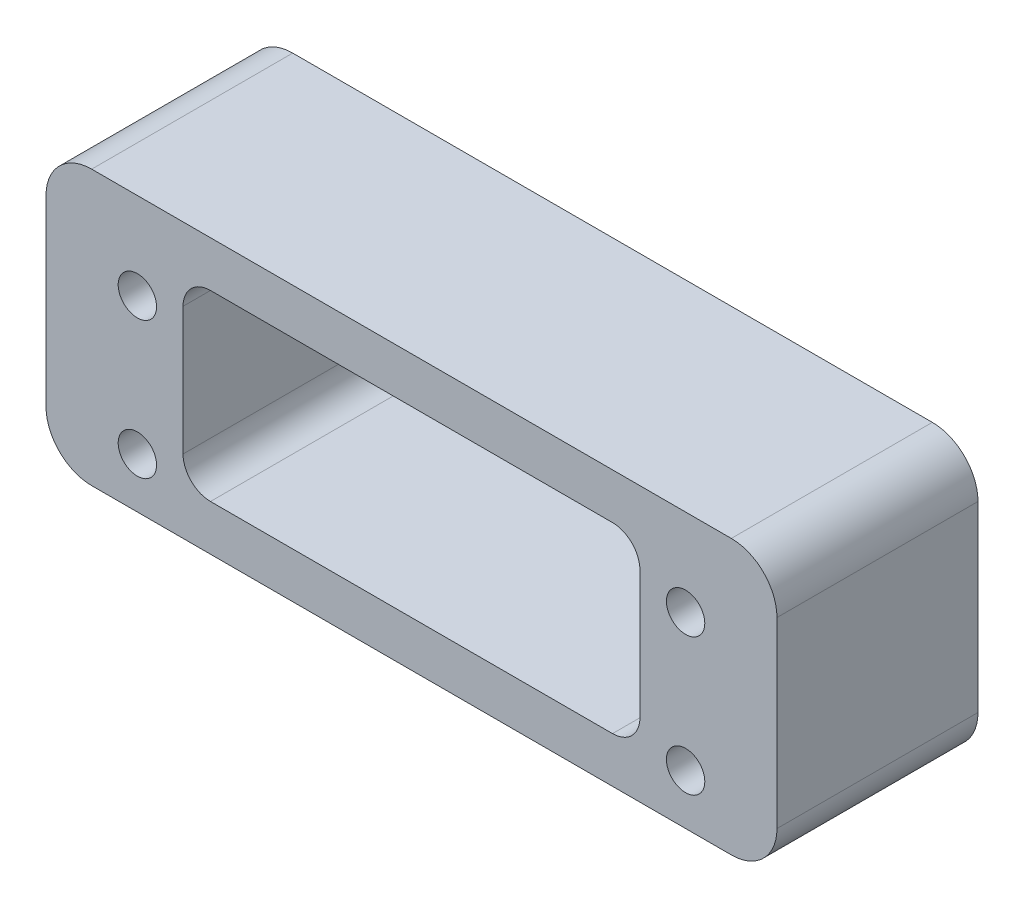
SolidWorks part; units mm, degrees
material "ABS"
ref_plane "前视基准面" through (0, 0, 0) normal (0, 0, 1) x (1, 0, 0)
ref_plane "上视基准面" through (0, 0, 0) normal (0, 1, 0) x (1, 0, 0)
ref_plane "右视基准面" through (0, 0, 0) normal (1, 0, 0) x (0, 0, -1)
sketch "草图1" plane through (0, 0, 0) normal (0, 0, 1) x (1, 0, 0)
  line L1 (-40, 15) -> (40, 15)
  line L2 (-40, 15) -> (-40, -15)
  line L3 (-40, -15) -> (40, -15)
  line L4 (40, 15) -> (40, -15)
  line L5 (-40, 15) -> (40, -15) construction
  line L6 (-40, -15) -> (40, 15) construction
  point P0 (0, 0)
  dimension "D1" = 80
  dimension "D2" = 30
extrude "凸台-拉伸1" add sketch "草图1" along normal mid plane 22
fillet "圆角1" radius 5 4 edges at (40, -15, 0) (-40, -15, 0) (-40, 15, 0) (40, 15, 0)
sketch "草图2" plane through (0, 0, 11) normal (0, 0, 1) x (1, 0, 0)
  line L0 (40, -10) -> (40, 10) construction
  line L1 (-35, -15) -> (35, -15) construction
  line L3 (-25, 10) -> (25, 10)
  line L4 (-25, 10) -> (-25, -10)
  line L5 (-25, -10) -> (25, -10)
  line L6 (25, 10) -> (25, -10)
  line L7 (-25, 10) -> (25, -10) construction
  line L8 (-25, -10) -> (25, 10) construction
  circle A0 centre (-30, 5.5) radius 2.1
  circle A1 centre (30, 5.5) radius 2.1
  circle A2 centre (30, -9.5) radius 2.1
  circle A3 centre (-30, -9.5) radius 2.1
  point P13 (0, 0)
  dimension "D1" = 4.2
  dimension "D2" = 10
  dimension "D3" = 70
  dimension "D4" = 5.5
  dimension "D5" = 20.5
  dimension "D6" = 50
  dimension "D7" = 20
extrude "切除-拉伸1" cut sketch "草图2" against normal through all
fillet "圆角2" radius 3 4 edges at (-25, -10, 0) (-25, 10, 0) (25, 10, 0) (25, -10, 0)
